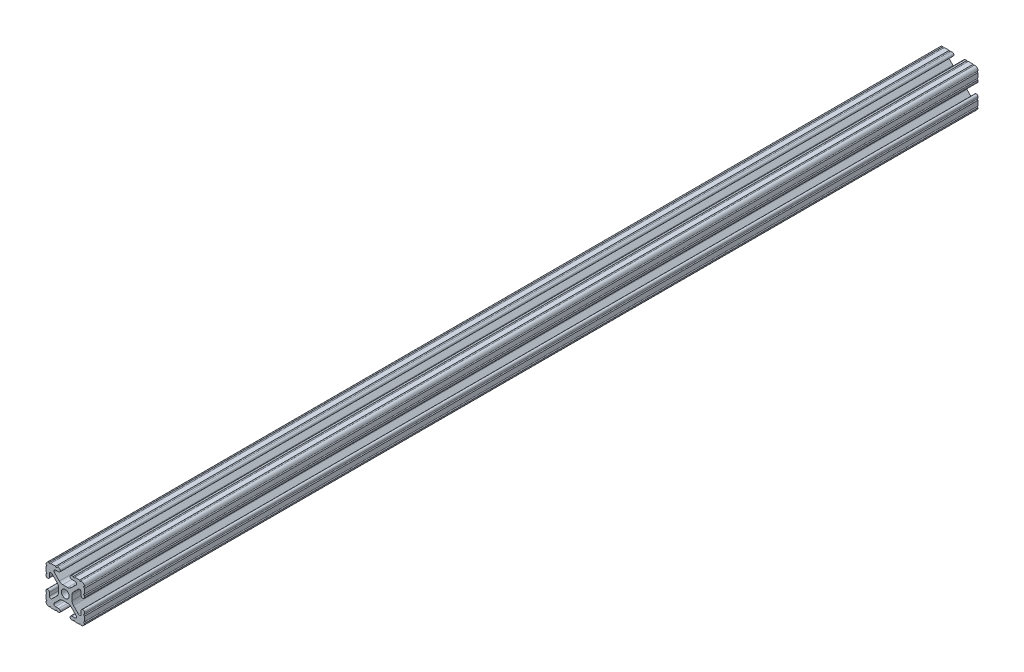
SolidWorks part; units mm, degrees
ref_plane "Front Plane" through (0, 0, 0) normal (0, 0, 1) x (1, 0, 0)
ref_plane "Top Plane" through (0, 0, 0) normal (0, 1, 0) x (1, 0, 0)
ref_plane "Right Plane" through (0, 0, 0) normal (1, 0, 0) x (0, 0, -1)
ref_plane "Plane1" through (0, 0, 590.55) normal (0, 0, 1) x (1, 0, 0)
sketch "Sketch1" plane through (0, 0, 590.55) normal (0, 0, 1) x (1, 0, 0)
  line L0 (-12.7, -6.3331) -> (-12.7, -9.5504)
  line L1 (-9.5504, -12.7) -> (-6.3331, -12.7)
  line L2 (-5.3171, -12.7) -> (-4.3434, -12.7)
  line L3 (-4.3434, -10.4902) -> (-6.4748, -10.4902)
  line L4 (-7.1932, -8.7558) -> (-3.8632, -5.4257)
  line L5 (-1.6181, -4.4958) -> (1.6181, -4.4958)
  line L6 (3.8632, -5.4257) -> (7.1932, -8.7558)
  line L7 (6.4748, -10.4902) -> (4.3434, -10.4902)
  line L8 (4.3434, -12.7) -> (5.3171, -12.7)
  line L9 (6.3331, -12.7) -> (9.5504, -12.7)
  line L10 (12.7, -9.5504) -> (12.7, -6.3331)
  line L11 (12.7, -5.3171) -> (12.7, -4.3434)
  line L12 (10.4902, -4.3434) -> (10.4902, -6.4748)
  line L13 (8.7558, -7.1932) -> (5.4257, -3.8632)
  line L14 (4.4958, -1.6181) -> (4.4958, 1.6181)
  line L15 (5.4257, 3.8632) -> (8.7558, 7.1932)
  line L16 (10.4902, 6.4748) -> (10.4902, 4.3434)
  line L17 (12.7, 4.3434) -> (12.7, 5.3171)
  line L18 (12.7, 6.3331) -> (12.7, 9.5504)
  line L19 (9.5504, 12.7) -> (6.3331, 12.7)
  line L20 (5.3171, 12.7) -> (4.3434, 12.7)
  line L21 (4.3434, 10.4902) -> (6.4748, 10.4902)
  line L22 (7.1932, 8.7558) -> (3.8632, 5.4257)
  line L23 (1.6181, 4.4958) -> (-1.6181, 4.4958)
  line L24 (-3.8632, 5.4257) -> (-7.1932, 8.7558)
  line L25 (-6.4748, 10.4902) -> (-4.3434, 10.4902)
  line L26 (-4.3434, 12.7) -> (-5.3171, 12.7)
  line L27 (-6.3331, 12.7) -> (-9.5504, 12.7)
  line L28 (-12.7, 9.5504) -> (-12.7, 6.3331)
  line L29 (-12.7, 5.3171) -> (-12.7, 4.3434)
  line L30 (-10.4902, 4.3434) -> (-10.4902, 6.4748)
  line L31 (-8.7558, 7.1932) -> (-5.4257, 3.8632)
  line L32 (-4.4958, 1.6181) -> (-4.4958, -1.6181)
  line L33 (-5.4257, -3.8632) -> (-8.7558, -7.1932)
  line L34 (-10.4902, -6.4748) -> (-10.4902, -4.3434)
  line L35 (-12.7, -4.3434) -> (-12.7, -5.3171)
  circle A0 centre (0, 0) radius 2.6035
  arc A1 (-12.7, -5.3171) -> (-12.7, -6.3331) centre (-12.7, -5.8251) cw
  arc A2 (-12.7, -9.5504) -> (-12.6998, -10.5664) centre (-12.7, -10.0584) cw
  arc A3 (-12.6998, -10.5664) -> (-10.5664, -12.6998) centre (-10.5918, -10.5918) ccw
  arc A4 (-10.5664, -12.6998) -> (-9.5504, -12.7) centre (-10.0584, -12.7) cw
  arc A5 (-6.3331, -12.7) -> (-5.3171, -12.7) centre (-5.8251, -12.7) cw
  arc A6 (-4.3434, -12.7) -> (-4.3434, -10.4902) centre (-4.3434, -11.5951) ccw
  arc A7 (-6.4748, -10.4902) -> (-7.1932, -8.7558) centre (-6.4748, -9.4742) cw
  arc A8 (-3.8632, -5.4257) -> (-1.6181, -4.4958) centre (-1.6181, -7.6708) cw
  arc A9 (1.6181, -4.4958) -> (3.8632, -5.4257) centre (1.6181, -7.6708) cw
  arc A10 (7.1932, -8.7558) -> (6.4748, -10.4902) centre (6.4748, -9.4742) cw
  arc A11 (4.3434, -10.4902) -> (4.3434, -12.7) centre (4.3434, -11.5951) ccw
  arc A12 (5.3171, -12.7) -> (6.3331, -12.7) centre (5.8251, -12.7) cw
  arc A13 (9.5504, -12.7) -> (10.5664, -12.6998) centre (10.0584, -12.7) cw
  arc A14 (10.5664, -12.6998) -> (12.6998, -10.5664) centre (10.5918, -10.5918) ccw
  arc A15 (12.6998, -10.5664) -> (12.7, -9.5504) centre (12.7, -10.0584) cw
  arc A16 (12.7, -6.3331) -> (12.7, -5.3171) centre (12.7, -5.8251) cw
  arc A17 (12.7, -4.3434) -> (10.4902, -4.3434) centre (11.5951, -4.3434) ccw
  arc A18 (10.4902, -6.4748) -> (8.7558, -7.1932) centre (9.4742, -6.4748) cw
  arc A19 (5.4257, -3.8632) -> (4.4958, -1.6181) centre (7.6708, -1.6181) cw
  arc A20 (4.4958, 1.6181) -> (5.4257, 3.8632) centre (7.6708, 1.6181) cw
  arc A21 (8.7558, 7.1932) -> (10.4902, 6.4748) centre (9.4742, 6.4748) cw
  arc A22 (10.4902, 4.3434) -> (12.7, 4.3434) centre (11.5951, 4.3434) ccw
  arc A23 (12.7, 5.3171) -> (12.7, 6.3331) centre (12.7, 5.8251) cw
  arc A24 (12.7, 9.5504) -> (12.6998, 10.5664) centre (12.7, 10.0584) cw
  arc A25 (12.6998, 10.5664) -> (10.5664, 12.6998) centre (10.5918, 10.5918) ccw
  arc A26 (10.5664, 12.6998) -> (9.5504, 12.7) centre (10.0584, 12.7) cw
  arc A27 (6.3331, 12.7) -> (5.3171, 12.7) centre (5.8251, 12.7) cw
  arc A28 (4.3434, 12.7) -> (4.3434, 10.4902) centre (4.3434, 11.5951) ccw
  arc A29 (6.4748, 10.4902) -> (7.1932, 8.7558) centre (6.4748, 9.4742) cw
  arc A30 (3.8632, 5.4257) -> (1.6181, 4.4958) centre (1.6181, 7.6708) cw
  arc A31 (-1.6181, 4.4958) -> (-3.8632, 5.4257) centre (-1.6181, 7.6708) cw
  arc A32 (-7.1932, 8.7558) -> (-6.4748, 10.4902) centre (-6.4748, 9.4742) cw
  arc A33 (-4.3434, 10.4902) -> (-4.3434, 12.7) centre (-4.3434, 11.5951) ccw
  arc A34 (-5.3171, 12.7) -> (-6.3331, 12.7) centre (-5.8251, 12.7) cw
  arc A35 (-9.5504, 12.7) -> (-10.5664, 12.6998) centre (-10.0584, 12.7) cw
  arc A36 (-10.5664, 12.6998) -> (-12.6998, 10.5664) centre (-10.5918, 10.5918) ccw
  arc A37 (-12.6998, 10.5664) -> (-12.7, 9.5504) centre (-12.7, 10.0584) cw
  arc A38 (-12.7, 6.3331) -> (-12.7, 5.3171) centre (-12.7, 5.8251) cw
  arc A39 (-12.7, 4.3434) -> (-10.4902, 4.3434) centre (-11.5951, 4.3434) ccw
  arc A40 (-10.4902, 6.4748) -> (-8.7558, 7.1932) centre (-9.4742, 6.4748) cw
  arc A41 (-5.4257, 3.8632) -> (-4.4958, 1.6181) centre (-7.6708, 1.6181) cw
  arc A42 (-4.4958, -1.6181) -> (-5.4257, -3.8632) centre (-7.6708, -1.6181) cw
  arc A43 (-8.7558, -7.1932) -> (-10.4902, -6.4748) centre (-9.4742, -6.4748) cw
  arc A44 (-10.4902, -4.3434) -> (-12.7, -4.3434) centre (-11.5951, -4.3434) ccw
extrude "Boss-Extrude1" add sketch "Sketch1" against normal blind 590.55
